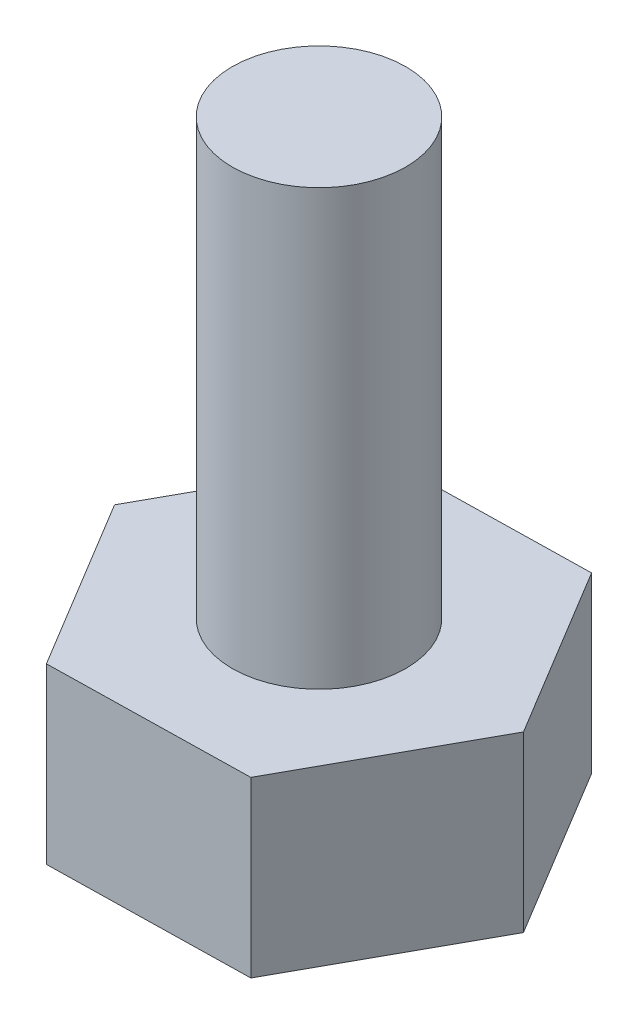
SolidWorks part; units mm, degrees
ref_plane "Front Plane" through (0, 0, 0) normal (0, 0, 1) x (1, 0, 0)
ref_plane "Top Plane" through (0, 0, 0) normal (0, 1, 0) x (1, 0, 0)
ref_plane "Right Plane" through (0, 0, 0) normal (1, 0, 0) x (0, 0, -1)
sketch "Sketch1" plane through (0, 0, 0) normal (0, 1, 0) x (1, 0, 0)
  circle A0 centre (-18.8764, -12.7107) radius 2
  dimension "D1" = 4
extrude "Boss-Extrude1" add sketch "Sketch1" along normal blind 10
sketch "Sketch2" plane through (0, 10, 0) normal (0, 1, 0) x (-1, 0, 0)
sketch "Sketch4" plane through (0, 0, 0) normal (0, -1, 0) x (1, 0, 0)
  line L1 (-16.4901, 16.6653) -> (-21.1081, 16.7546)
  line L2 (-21.1081, 16.7546) -> (-23.4943, 12.7999)
  line L3 (-23.4943, 12.7999) -> (-21.2627, 8.756)
  line L4 (-21.2627, 8.756) -> (-16.6447, 8.6668)
  line L5 (-16.6447, 8.6668) -> (-14.2585, 12.6214)
  line L6 (-14.2585, 12.6214) -> (-16.4901, 16.6653)
  circle A0 centre (-18.8764, 12.7107) radius 4 construction
  circle A1 centre (-18.8764, 12.7107) radius 2 construction
  dimension "D1" = 4
  dimension "D2" = 4
  dimension "D3" = 4
extrude "Boss-Extrude4" add sketch "Sketch4" along normal blind 4
